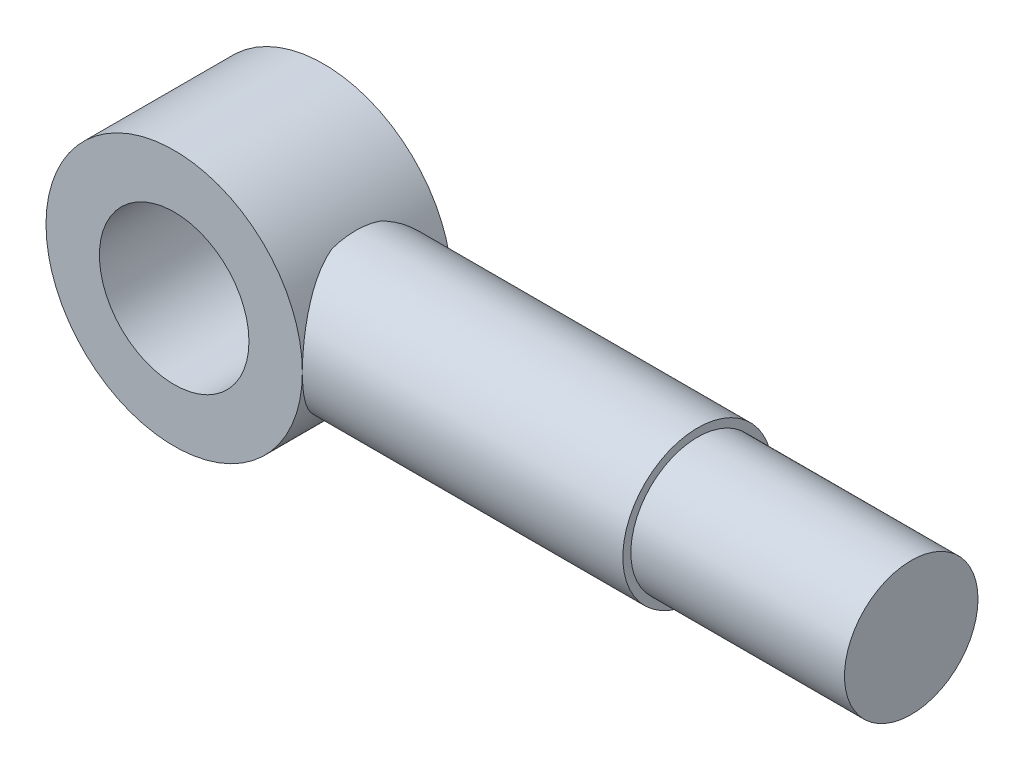
SolidWorks part; units mm, degrees
ref_plane "Front Plane" through (0, 0, 0) normal (0, 0, 1) x (1, 0, 0)
ref_plane "Top Plane" through (0, 0, 0) normal (0, 1, 0) x (1, 0, 0)
ref_plane "Right Plane" through (0, 0, 0) normal (1, 0, 0) x (0, 0, -1)
sketch "Sketch1" plane through (0, 0, 0) normal (0, 0, 1) x (1, 0, 0)
  line L1 (0, -56.6234) -> (0, 71.5152) construction
  circle A0 centre (0, 0) radius 24
  circle A1 centre (0, 0) radius 14
  dimension "D1" = 28
  dimension "D2" = 48
extrude "Boss-Extrude3" add sketch "Sketch1" along normal mid plane 28 contours A1 | A0
sketch "Sketch5" plane through (0, 0, 0) normal (1, 0, 0) x (0, 0, -1)
  circle A0 centre (0, 0) radius 14
  dimension "D1" = 28
extrude "Boss-Extrude7" add sketch "Sketch5" along normal blind 64 from offset 20 contours A0
sketch "Sketch7" plane through (84, 0, 0) normal (1, 0, 0) x (0, 0, -1)
  circle A0 centre (0, 0) radius 12.5
  dimension "D1" = 25
extrude "Boss-Extrude8" add sketch "Sketch7" along normal blind 40 contours A0
